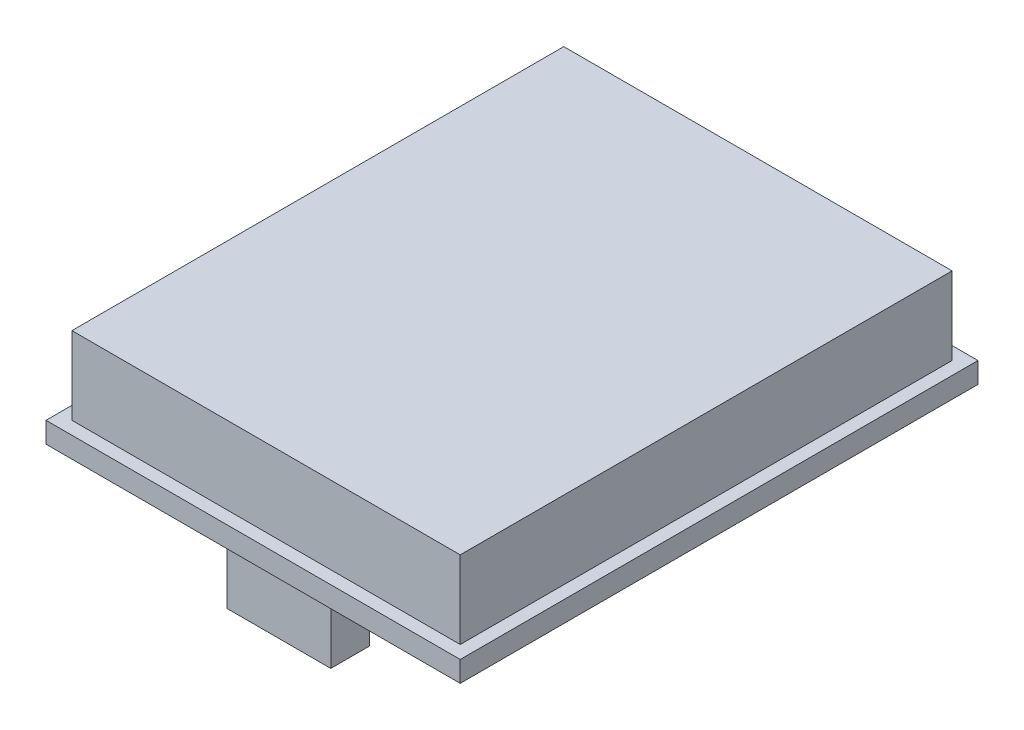
SolidWorks part; units mm, degrees
ref_plane "Front Plane" through (0, 0, 0) normal (0, 0, 1) x (1, 0, 0)
ref_plane "Top Plane" through (0, 0, 0) normal (0, 1, 0) x (1, 0, 0)
ref_plane "Right Plane" through (0, 0, 0) normal (1, 0, 0) x (0, 0, -1)
sketch "Sketch1" plane through (0, 0, 0) normal (0, 1, 0) x (1, 0, 0)
  line L1 (0, 0) -> (32, 0)
  line L2 (0, 0) -> (0, 40)
  line L3 (0, 40) -> (32, 40)
  line L4 (32, 0) -> (32, 40)
  dimension "D1" = 40
  dimension "D2" = 32
extrude "Boss-Extrude1" add sketch "Sketch1" along normal blind 1.6
sketch "Sketch2" plane through (0, 1.6, 0) normal (0, 1, 0) x (1, 0, 0)
  line L14 (31, 1) -> (31, 39)
  line L15 (1, 1) -> (31, 1)
  line L16 (1, 39) -> (1, 1)
  line L17 (31, 39) -> (1, 39)
  line L18 (31, 1) -> (31, 39)
  line L19 (1, 1) -> (31, 1)
  line L20 (1, 39) -> (1, 1)
  line L21 (31, 39) -> (1, 39)
  dimension "D1" = 1
extrude "Boss-Extrude2" add sketch "Sketch2" along normal blind 6
sketch "Sketch3" plane through (0, 0, 0) normal (0, -1, 0) x (1, 0, 0)
  line L0 (0, 0) -> (12, -2) construction
  line L1 (12, -2) -> (20, -2)
  line L2 (12, -2) -> (12, -5)
  line L3 (12, -5) -> (20, -5)
  line L4 (20, -2) -> (20, -5)
  line L5 (20, -2) -> (32, 0) construction
  line L6 (0, 0) -> (32, 0) construction
  dimension "D1" = 8
  dimension "D2" = 2
  dimension "D3" = 3
extrude "Boss-Extrude3" add sketch "Sketch3" along normal blind 6
